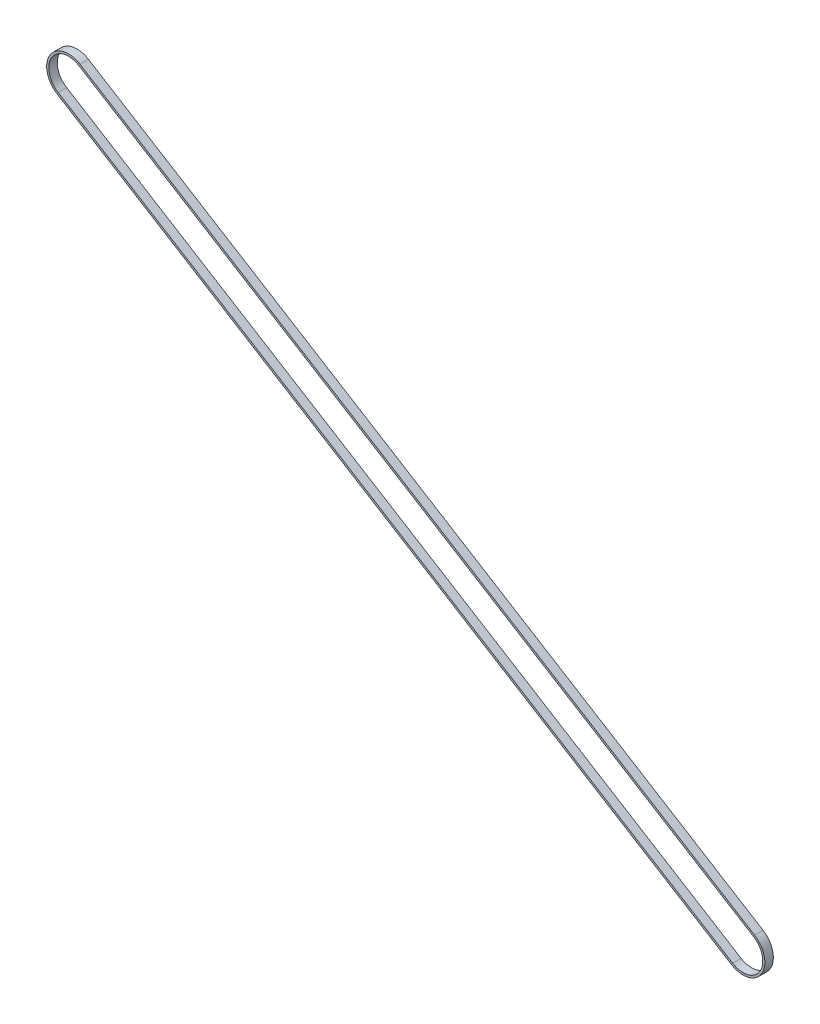
SolidWorks part; units mm, degrees
ref_plane "前视基准面" through (0, 0, 0) normal (0, 0, 1) x (1, 0, 0)
ref_plane "上视基准面" through (0, 0, 0) normal (0, 1, 0) x (1, 0, 0)
ref_plane "右视基准面" through (0, 0, 0) normal (1, 0, 0) x (0, 0, -1)
sketch "草图2" plane through (0, 0, 0) normal (0, 0, 1) x (1, 0, 0)
  line L0 (0, 0) -> (1, 0) construction
  line L1 (0, 0) -> (0, 1) construction
  line L2 (-7.3468, -11.888) -> (-485.2662, 283.4673)
  line L3 (-470.5726, 307.2433) -> (7.3468, 11.888)
  arc A0 (7.3468, 11.888) -> (-7.3468, -11.888) centre (0, 0) cw
  arc A1 (-485.2662, 283.4673) -> (-470.5726, 307.2433) centre (-477.9194, 295.3553) cw
extrude "拉伸-薄壁1" add sketch "草图2" along normal blind 6 thin thin type one direction wall 1.5
